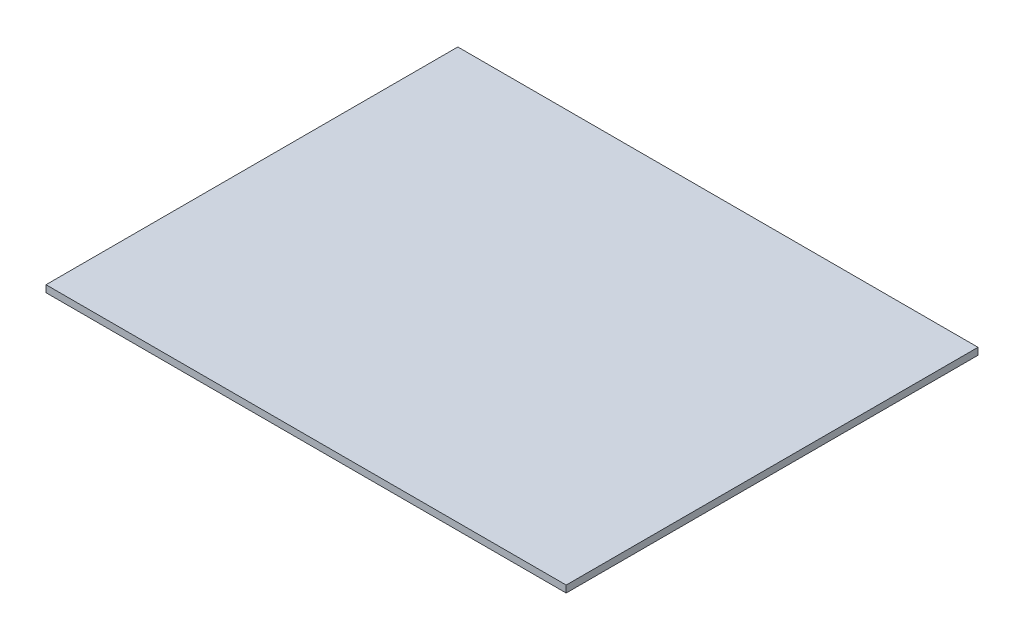
SolidWorks part; units mm, degrees
ref_plane "Front Plane" through (0, 0, 0) normal (0, 0, 1) x (1, 0, 0)
ref_plane "Top Plane" through (0, 0, 0) normal (0, 1, 0) x (1, 0, 0)
ref_plane "Right Plane" through (0, 0, 0) normal (1, 0, 0) x (0, 0, -1)
sketch "Sketch1" plane through (0, 0, 0) normal (0, 1, 0) x (1, 0, 0)
  line L1 (0, 0) -> (1200, 0)
  line L2 (0, 0) -> (0, 950)
  line L3 (0, 950) -> (1200, 950)
  line L4 (1200, 0) -> (1200, 950)
  dimension "D1" = 1200
  dimension "D2" = 950
extrude "Boss-Extrude1" add sketch "Sketch1" along normal blind 16 contours L2 L1 L4 L3
